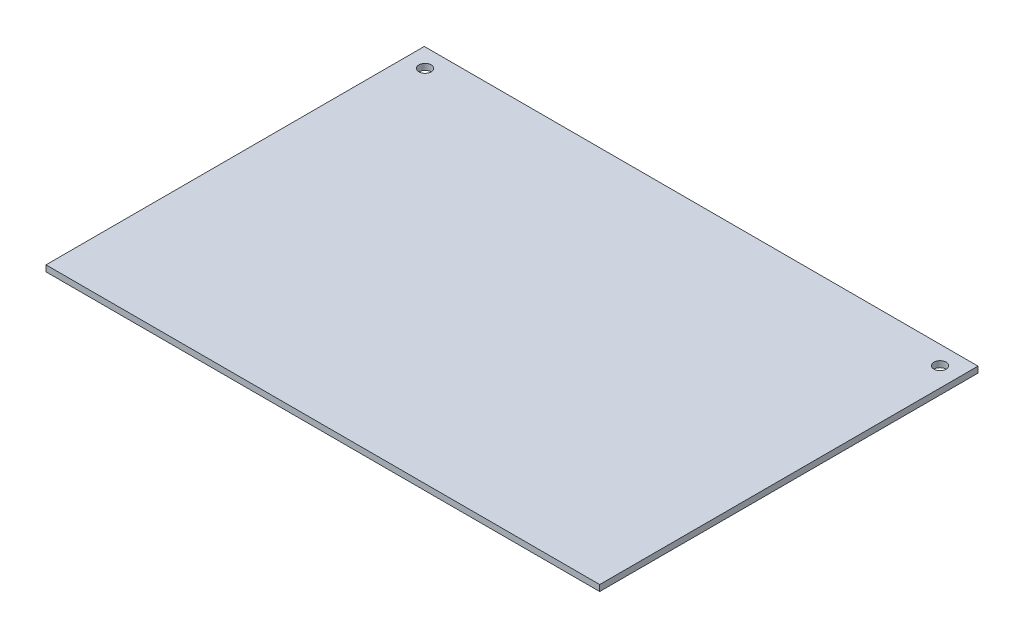
SolidWorks part; units mm, degrees
ref_plane "Front Plane" through (0, 0, 0) normal (0, 0, 1) x (1, 0, 0)
ref_plane "Top Plane" through (0, 0, 0) normal (0, 1, 0) x (1, 0, 0)
ref_plane "Right Plane" through (0, 0, 0) normal (1, 0, 0) x (0, 0, -1)
sketch "Sketch1" plane through (0, 0, 0) normal (0, 1, 0) x (1, 0, 0)
  line L1 (-90.75, -62) -> (90.75, -62)
  line L2 (-90.75, -62) -> (-90.75, 62)
  line L3 (-90.75, 62) -> (90.75, 62)
  line L4 (90.75, -62) -> (90.75, 62)
  line L5 (-90.75, -62) -> (90.75, 62) construction
  line L6 (-90.75, 62) -> (90.75, -62) construction
  point P0 (0, 0)
  dimension "D1" = 124
  dimension "D2" = 181.5
extrude "Boss-Extrude1" add sketch "Sketch1" along normal blind 2
sketch "Sketch2" plane through (0, 2, 0) normal (0, 1, 0) x (1, 0, 0)
  line L0 (1.2065, -4.4237) -> (353.8731, -4.4237) construction
sketch "Sketch3" plane through (0, 2, 0) normal (0, 1, 0) x (1, 0, 0)
  line L0 (84.4007, 55.9051) -> (-84.4007, 55.9051) construction
  line L1 (-90.75, 62) -> (90.75, 62) construction
  circle A0 centre (-84.4007, 55.9051) radius 2
  circle A1 centre (84.4007, 55.9051) radius 2
  point P0 (-84.4007, 55.9051)
  point P1 (84.4007, 55.9051)
  point P8 (0, 62)
  point P9 (0, 55.9051)
  dimension "D1" = 4
extrude "Cut-Extrude1" cut sketch "Sketch3" against normal through all
sketch "Sketch4" plane through (0, 2, 0) normal (0, 1, 0) x (1, 0, 0)
  line L0 (-31.8614, -4.2563) -> (-31.8614, -62) construction
  line L1 (-90.75, -62) -> (90.75, -62) construction
sketch "Sketch5" plane through (0, 2, 0) normal (0, 1, 0) x (1, 0, 0)
  line L0 (-77.0137, -26.2186) -> (-44.5115, -26.2186) construction
  line L1 (-60.7626, -26.2186) -> (-60.7626, -62) construction
  line L2 (-90.75, -62) -> (90.75, -62) construction
sketch "Sketch6" plane through (90.75, 0, 0) normal (1, 0, 0) x (0, 0, -1)
  line L0 (-535.6809, 98.8487) -> (-54.9222, 75.3357) construction
